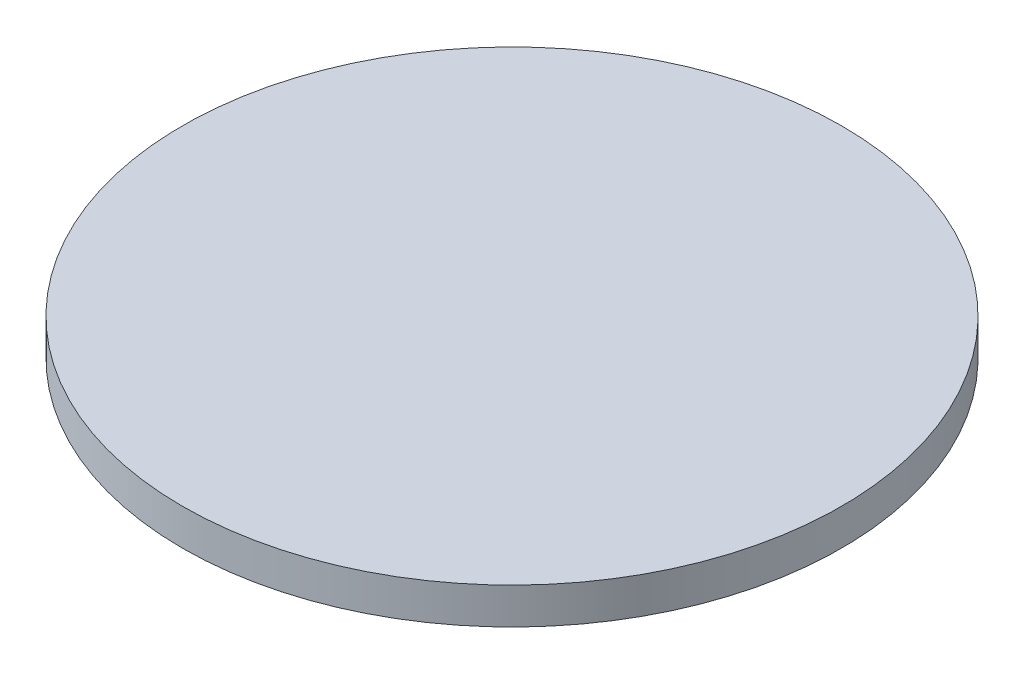
SolidWorks part; units mm, degrees
ref_plane "Front Plane" through (0, 0, 0) normal (0, 0, 1) x (1, 0, 0)
ref_plane "Top Plane" through (0, 0, 0) normal (0, 1, 0) x (1, 0, 0)
ref_plane "Right Plane" through (0, 0, 0) normal (1, 0, 0) x (0, 0, -1)
sketch "Sketch1" plane through (0, 0, 0) normal (0, 1, 0) x (1, 0, 0)
  circle A0 centre (0, 0) radius 27.225
  dimension "D1" = 54.45
extrude "Boss-Extrude1" add sketch "Sketch1" along normal blind 3
